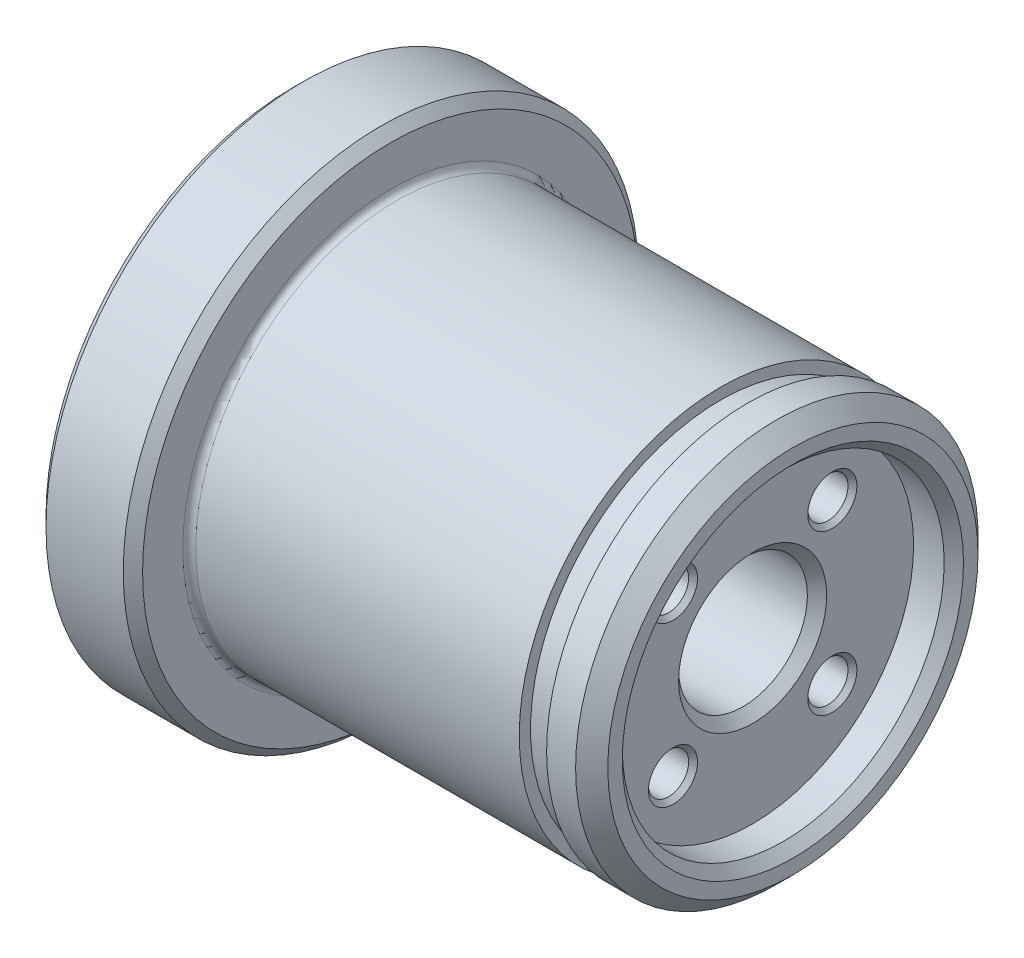
SolidWorks part; units mm, degrees
material "1060 Сплав"
ref_plane "Спереди" through (0, 0, 0) normal (0, 0, 1) x (1, 0, 0)
ref_plane "Сверху" through (0, 0, 0) normal (0, 1, 0) x (1, 0, 0)
ref_plane "Справа" through (0, 0, 0) normal (1, 0, 0) x (0, 0, -1)
sketch "Эскиз1" plane through (0, 0, 0) normal (0, 0, 1) x (1, 0, 0)
  line L0 (0, 0) -> (22138.4448, 0) construction
  line L1 (0, 0) -> (0, 12.5)
  line L2 (0, 12.5) -> (-25, 12.5)
  line L3 (-25, 12.5) -> (-25, 16)
  line L4 (-25, 16) -> (-31, 16)
  line L5 (-31, 16) -> (-31, 0)
  line L8 (0, 0) -> (-31, 0)
  dimension "D1" = 31
  dimension "D2" = 6
  dimension "D3" = 25
  dimension "D6" = 32
revolve "Повернуть1" add sketch "Эскиз1" angle 360 about L0
sketch "Эскиз2" plane through (0, 0, 0) normal (0, 0, 1) x (1, 0, 0)
  line L0 (-4.5, 12.5) -> (-4.5, 11.8)
  line L1 (-4.5, 12.5) -> (-24.6, 12.5) construction
  line L2 (-4.5, 11.8) -> (-2.8, 11.8)
  line L3 (-2.8, 11.8) -> (-2.8, 12.5)
  line L4 (-2.8, 12.5) -> (-4.5, 12.5)
  line L5 (0, -12.5) -> (0, 12.5) construction
  line L6 (0, 0) -> (-50000, 0) construction
  point P10 (-2.8, 12.15)
  point P13 (0, 0)
  dimension "D1" = 4.5
  dimension "D2" = 1.7
  dimension "D3" = 23.6
revolve "Вырез-Повернуть1" cut sketch "Эскиз2" angle 360 about L6
chamfer "Фаска1" distance 1 angle 45 1 edges at (0, 0, 12.5)
fillet "Скругление1" radius 0.4 1 edges at (-25, 0, 12.5)
sketch "Эскиз5" plane through (0, 0, 0) normal (0, 0, 1) x (1, 0, 0)
  line L0 (0, 0) -> (0, 10)
  line L1 (0, -11.5) -> (0, 11.5) construction
  line L7 (0, 10) -> (-2.5, 10)
  line L8 (-2.5, 10) -> (-2.5, 0)
  line L9 (-2.5, 0) -> (0, 0)
  line L10 (0, 0) -> (-50000, 0) construction
  dimension "D1" = 2.5
  dimension "D2" = 20
revolve "Вырез-Повернуть2" cut sketch "Эскиз5" angle 360 about L10
hole_wizard "Отверстие обработанное метчиком M31" positions "Эскиз3" profile "Эскиз4" tap size "M3" standard "DIN"
sketch "Эскиз3" plane through (-2.5, 0, 0) normal (1, 0, 0) x (0, 0, -1)
  line L0 (0, 0) -> (0, 7) construction
  line L2 (0, 0) -> (4.9497, 4.9497) construction
  circle A0 centre (0, 0) radius 7 construction
  point P0 (4.9497, 4.9497)
  dimension "D1" = 14
  dimension "D2" = 45
cosmetic thread "Отверстие резьбы1" parameters "D1"=6, "D2"=3
sketch "Эскиз4" plane through (-2.5, 4.9497, -4.9497) normal (0, 1, 0) x (0, 0, -1)
  line L0 (0, 0) -> (0, 7.7511)
  line L1 (0, 7.7511) -> (1.25, 7)
  line L2 (1.25, 7) -> (1.25, 0.275)
  line L3 (1.25, 0.275) -> (1.525, 0)
  line L5 (1.525, 0) -> (0, 0)
  line L6 (-1.25, 0.275) -> (-1.525, 0) construction
  line L10 (0, 7.7511) -> (-1.25, 7) construction
  line L11 (0, -6.35) -> (0, 107.95) construction
  dimension "Диаметр сверла" = 2.5
  dimension "Глубина сверла" = 7
  dimension "Диаметр передней зенковки" = 3.05
  dimension "Угол передней зенковки" = 90
  dimension "Угол заточки сверла" = 118
pattern_circular "Круговой массив1" count 4 over 360 about axis through (0, 0, 0) along (1, 0, 0) of "Отверстие обработанное метчиком M31"
chamfer "Фаска2" distance 0.6 angle 45 1 edges at (0, 0, -10)
sketch "Эскиз6" plane through (0, 0, 0) normal (0, 0, 1) x (1, 0, 0)
  line L0 (0, 0) -> (-50000, 0) construction
  line L1 (-31, 0) -> (-31, 4)
  line L2 (-31, 16) -> (-31, -16) construction
  line L3 (-31, 4) -> (0, 4)
  line L4 (0, -11.5) -> (0, 11.5) construction
  line L5 (0, 4) -> (0, 0)
  line L6 (0, 0) -> (-31, 0)
  dimension "D1" = 8
revolve "Вырез-Повернуть3" cut sketch "Эскиз6" angle 360 about L0
chamfer "Фаска3" distance 0.6 angle 45 2 edges at (-31, 0, -4) (-2.5, 0, 4)
hole_wizard "Отверстие обработанное метчиком M32" positions "Эскиз7" profile "Эскиз8" tap size "M3" standard "DIN"
sketch "Эскиз7" plane through (-31, 0, 0) normal (-1, 0, 0) x (0, 0, 1)
  line L0 (0, 16) -> (0, -16) construction
  line L2 (-16, 0) -> (16, 0) construction
  line L4 (0, 0) -> (11.3137, 11.3137) construction
  circle A0 centre (0, 0) radius 16 construction
  circle A1 centre (0, 0) radius 10 construction
  point P0 (7.0711, 7.0711)
  point P22 (6.9973, 6.9973)
  point P23 (7.0711, 7.0711)
  dimension "D1" = 20
  dimension "D2" = 45
sketch "Эскиз8" plane through (-31, 7.0711, 7.0711) normal (0, 1, 0) x (0, 0, 1)
  line L0 (0, 0) -> (0, 8.7511)
  line L1 (0, 8.7511) -> (1.25, 8)
  line L2 (1.25, 8) -> (1.25, 0.275)
  line L3 (1.25, 0.275) -> (1.525, 0)
  line L5 (1.525, 0) -> (0, 0)
  line L6 (-1.25, 0.275) -> (-1.525, 0) construction
  line L10 (0, 8.7511) -> (-1.25, 8) construction
  line L11 (0, -6.35) -> (0, 107.95) construction
  dimension "Диаметр сверла" = 2.5
  dimension "Глубина сверла" = 8
  dimension "Диаметр передней зенковки" = 3.05
  dimension "Угол передней зенковки" = 90
  dimension "Угол заточки сверла" = 118
cosmetic thread "Отверстие резьбы2" parameters "D1"=6, "D2"=3
pattern_circular "Круговой массив2" count 4 over 360 about axis through (0, 0, 0) along (1, 0, 0) of "Отверстие обработанное метчиком M32"
chamfer "Фаска4" distance 0.6 angle 45 2 edges at (-31, 0, 16) (-25, 0, 16)
